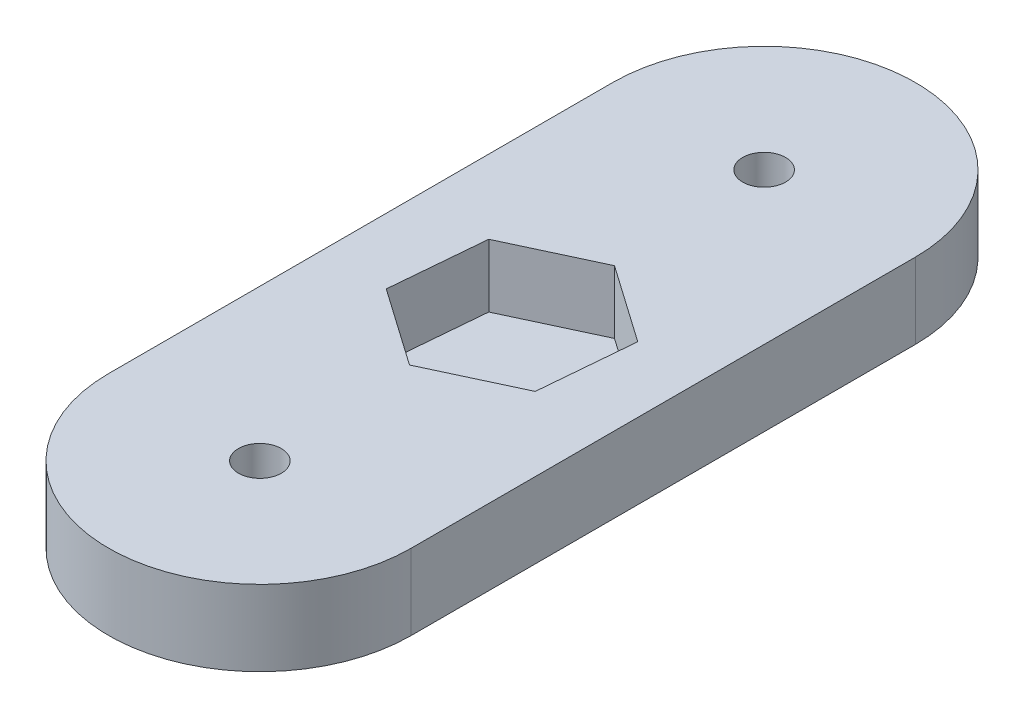
SolidWorks part; units mm, degrees
material "ABS PC"
ref_plane "Front Plane" through (0, 0, 0) normal (0, 0, 1) x (1, 0, 0)
ref_plane "Top Plane" through (0, 0, 0) normal (0, 1, 0) x (1, 0, 0)
ref_plane "Right Plane" through (0, 0, 0) normal (1, 0, 0) x (0, 0, -1)
sketch "Sketch1" plane through (0, 0, 0) normal (0, 1, 0) x (1, 0, 0)
  line L0 (0, 0) -> (0, 40) construction
  line L1 (-12, 0) -> (-12, 40)
  line L2 (12, 0) -> (12, 40)
  arc A0 (-12, 0) -> (12, 0) centre (0, 0) ccw
  arc A1 (12, 40) -> (-12, 40) centre (0, 40) ccw
  circle A2 centre (0, 40) radius 1.7
  circle A3 centre (0, 0) radius 1.7
  point P3 (0, 20)
  dimension "D2" = 40
  dimension "D3" = 3.4
  dimension "D1" = 24
extrude "Boss-Extrude1" add sketch "Sketch1" along normal blind 6
sketch "Sketch2" plane through (0, 6, 0) normal (0, 1, 0) x (1, 0, 0)
  line L0 (12, 0) -> (12, 40) construction
  line L1 (6.1482, 15.695) -> (6.8023, 23.172)
  line L2 (6.8023, 23.172) -> (0.6542, 27.477)
  line L3 (0.6542, 27.477) -> (-6.1482, 24.305)
  line L4 (-6.1482, 24.305) -> (-6.8023, 16.828)
  line L5 (-6.8023, 16.828) -> (-0.6542, 12.523)
  line L6 (-0.6542, 12.523) -> (6.1482, 15.695)
  line L7 (-12, 40) -> (-12, 0) construction
  circle A0 centre (0, 20) radius 6.5 construction
  dimension "D1" = 13
  dimension "D2" = 12
  dimension "D3" = 20
  dimension "D4" = 115
extrude "Cut-Extrude1" cut sketch "Sketch2" against normal blind 5
